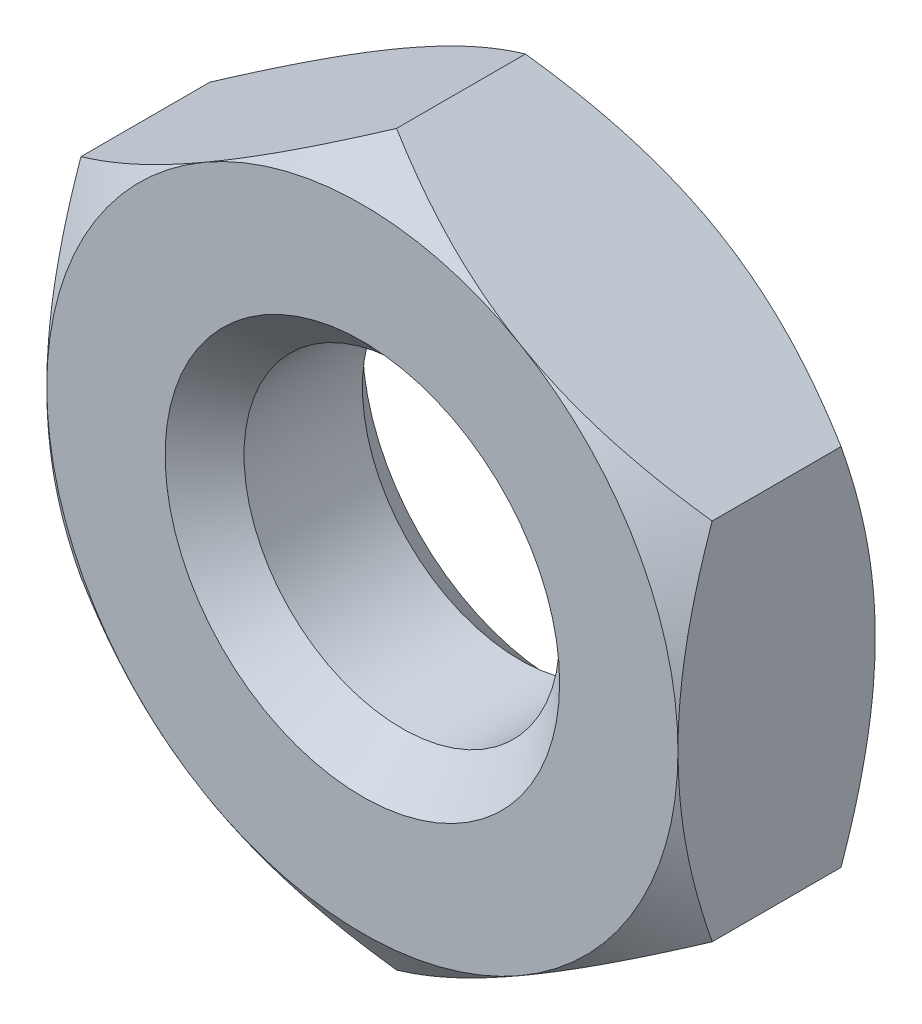
SolidWorks part; units mm, degrees
ref_plane "Front Plane" through (0, 0, 0) normal (0, 0, 1) x (1, 0, 0)
ref_plane "Top Plane" through (0, 0, 0) normal (0, 1, 0) x (1, 0, 0)
ref_plane "Right Plane" through (0, 0, 0) normal (1, 0, 0) x (0, 0, -1)
sketch "Sketch1" plane through (0, 0, 0) normal (0, 0, 1) x (1, 0, 0)
  line L1 (-8, 4.6188) -> (-8, -4.6188)
  line L2 (-8, -4.6188) -> (0, -9.2376)
  line L3 (0, -9.2376) -> (8, -4.6188)
  line L4 (8, -4.6188) -> (8, 4.6188)
  line L5 (8, 4.6188) -> (0, 9.2376)
  line L6 (0, 9.2376) -> (-8, 4.6188)
  circle A0 centre (0, 0) radius 8 construction
  circle A1 centre (0, 0) radius 4
  dimension "D2" = 8
  dimension "D1" = 16
extrude "Boss-Extrude1" add sketch "Sketch1" along normal mid plane 5
sketch "Sketch2" plane through (0, 0, 2.5) normal (0, 0, 1) x (1, 0, 0)
  line L0 (0, 9.2376) -> (-8, 4.6188) construction
  circle A0 centre (0, 0) radius 8
extrude "Cut-Extrude1" cut sketch "Sketch2" against normal through all draft 55 flip side to cut
mirror "Mirror1" about plane through (0, 0, 0) normal (0, 0, 1) of "Cut-Extrude1"
chamfer "Chamfer1" distance 1 angle 45 2 edges at (4, 0, -2.5) (4, 0, 2.5)
